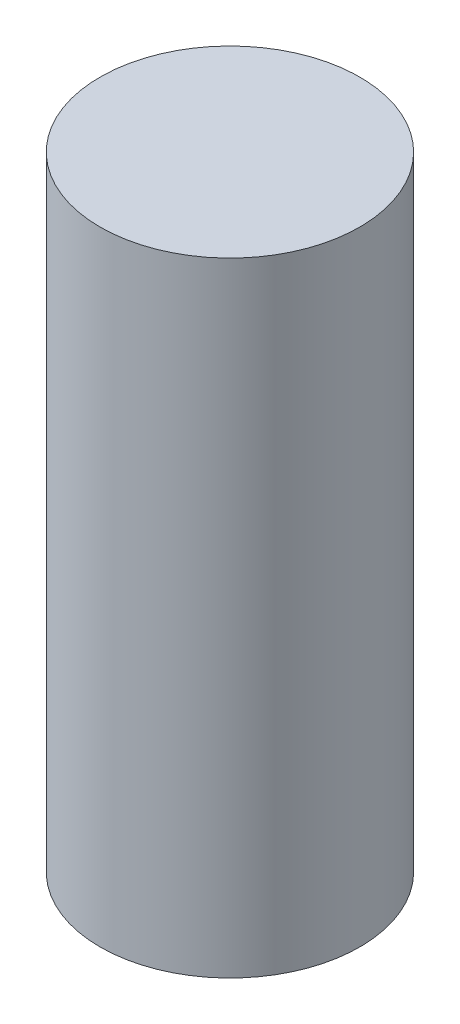
SolidWorks part; units mm, degrees
ref_plane "Front Plane" through (0, 0, 0) normal (0, 0, 1) x (1, 0, 0)
ref_plane "Top Plane" through (0, 0, 0) normal (0, 1, 0) x (1, 0, 0)
ref_plane "Right Plane" through (0, 0, 0) normal (1, 0, 0) x (0, 0, -1)
sketch "Sketch1" plane through (0, 0, 0) normal (0, 1, 0) x (1, 0, 0)
  circle A0 centre (0, 0) radius 12.5
  dimension "D1" = 25
extrude "Boss-Extrude1" add sketch "Sketch1" along normal blind 60
